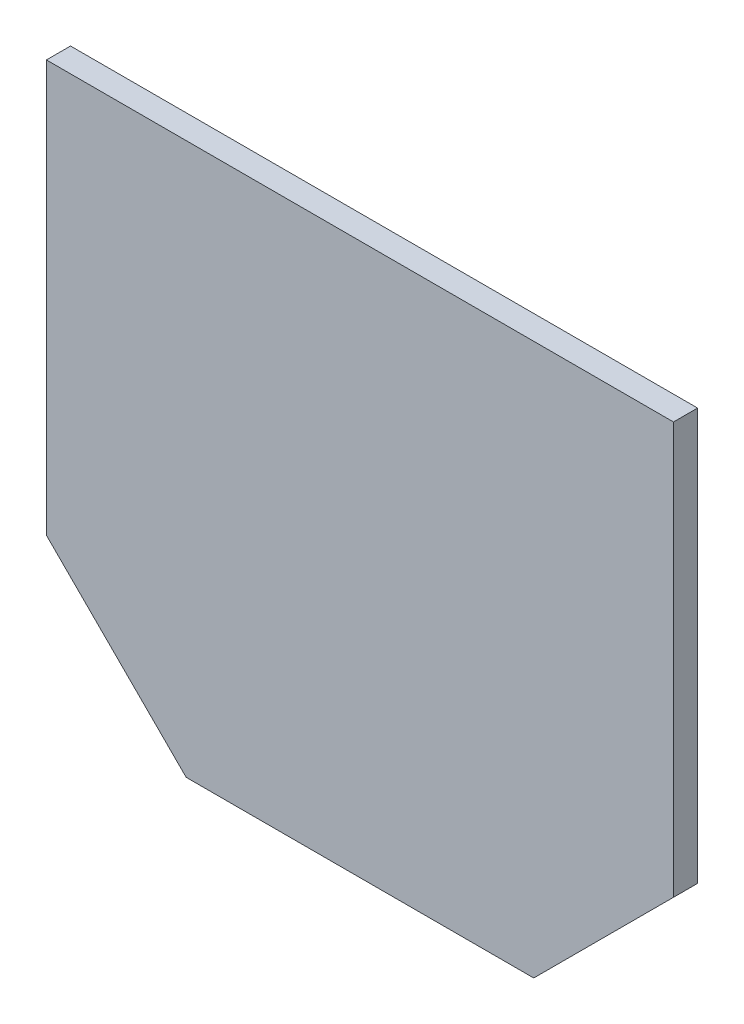
SolidWorks part; units mm, degrees
ref_plane "Front Plane" through (0, 0, 0) normal (0, 0, 1) x (1, 0, 0)
ref_plane "Top Plane" through (0, 0, 0) normal (0, 1, 0) x (1, 0, 0)
ref_plane "Right Plane" through (0, 0, 0) normal (1, 0, 0) x (0, 0, -1)
sketch "Sketch2" plane through (0, 0, 0) normal (0, 0, 1) x (1, 0, 0)
  line L0 (0, 0) -> (183.134, 0)
  line L1 (183.134, 0) -> (256.7721, 73.6381)
  line L2 (256.7721, 73.6381) -> (256.7721, 290.5541)
  line L3 (256.7721, 290.5541) -> (-73.6381, 290.5541)
  line L4 (-73.6381, 290.5541) -> (-73.6381, 73.6381)
  line L5 (-73.6381, 73.6381) -> (0, 0)
  dimension "D1" = 135
  dimension "D2" = 183.134
  dimension "D3" = 216.916
  dimension "D4" = 104.14
extrude "Boss-Extrude1" add sketch "Sketch2" along normal blind 12.7
